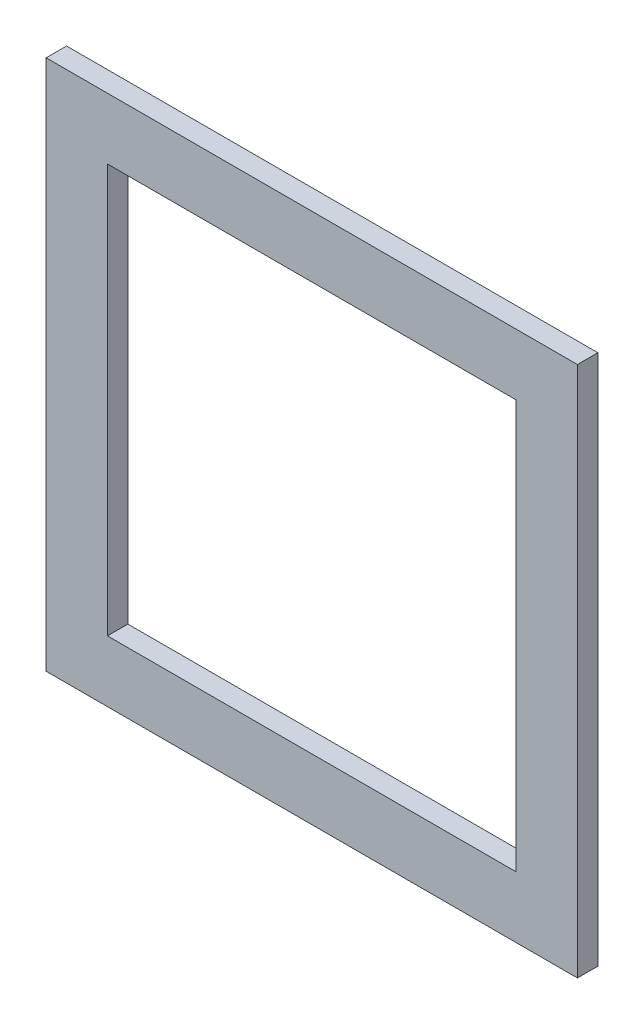
SolidWorks part; units mm, degrees
ref_plane "Piano frontale" through (0, 0, 0) normal (0, 0, 1) x (1, 0, 0)
ref_plane "Piano superiore" through (0, 0, 0) normal (0, 1, 0) x (1, 0, 0)
ref_plane "Piano destro" through (0, 0, 0) normal (1, 0, 0) x (0, 0, -1)
sketch "Schizzo1" plane through (0, 0, 0) normal (0, 0, 1) x (1, 0, 0)
  line L1 (65, 65) -> (-65, 65)
  line L2 (65, 65) -> (65, -65)
  line L3 (65, -65) -> (-65, -65)
  line L4 (-65, 65) -> (-65, -65)
  line L5 (65, 65) -> (-65, -65) construction
  line L6 (65, -65) -> (-65, 65) construction
  point P0 (0, 0)
  dimension "D1" = 130
  dimension "D2" = 130
extrude "Estrusione-Estrusione1" add sketch "Schizzo1" along normal blind 5
sketch "Schizzo2" plane through (0, 0, 5) normal (0, 0, 1) x (1, 0, 0)
  line L0 (65, 65) -> (-65, 65) construction
  line L1 (50, 50) -> (-50, 50)
  line L2 (50, 50) -> (50, -50)
  line L3 (50, -50) -> (-50, -50)
  line L4 (-50, 50) -> (-50, -50)
  line L5 (50, 50) -> (-50, -50) construction
  line L6 (50, -50) -> (-50, 50) construction
  line L7 (65, -65) -> (65, 65) construction
  point P0 (0, 0)
  dimension "D1" = 15
  dimension "D2" = 15
extrude "Taglio-Estrusione1" cut sketch "Schizzo2" against normal blind 5
